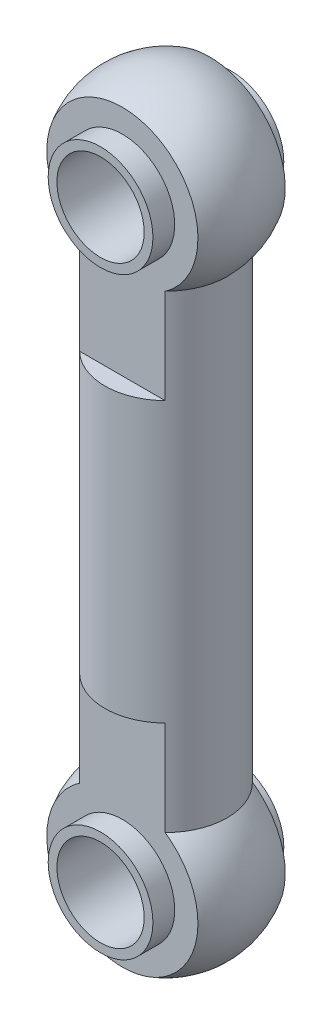
SolidWorks part; units mm, degrees
ref_plane "Front Plane" through (0, 0, 0) normal (0, 0, 1) x (1, 0, 0)
ref_plane "Top Plane" through (0, 0, 0) normal (0, 1, 0) x (1, 0, 0)
ref_plane "Right Plane" through (0, 0, 0) normal (1, 0, 0) x (0, 0, -1)
sketch "Sketch1" plane through (0, 0, 0) normal (0, 0, 1) x (1, 0, 0)
  line L0 (0, 0) -> (0, -7)
  line L1 (1.75, -17) -> (3.5, -17)
  line L2 (3.5, -17) -> (3.5, -3.5707)
  line L3 (0, 0) -> (0, 5)
  line L7 (0, -7) -> (1.75, -7)
  line L8 (1.75, -17) -> (1.75, -7)
  arc A0 (3.5, -3.5707) -> (0, 5) centre (0, 0) ccw
  dimension "D1" = 5
  dimension "D2" = 22
  dimension "D3" = 3.5
  dimension "D4" = 10
  dimension "D5" = 1.75
revolve "Revolve1" add sketch "Sketch1" angle 360 about L3
sketch "Sketch2" plane through (0, 0, 0) normal (0, 0, 1) x (1, 0, 0)
  circle A0 centre (0, 0) radius 2.5
  dimension "D1" = 5
extrude "Cut-Extrude1" cut sketch "Sketch2" against normal through all both and the other way through all
sketch "Sketch3" plane through (0, 0, 0) normal (0, 0, 1) x (1, 0, 0)
  circle A0 centre (0, 0) radius 2.5
ref_plane "Plane1" through (0, 0, 2.5) normal (0, 0, 1) x (1, 0, 0)
sketch "Sketch4" plane through (0, 0, 2.5) normal (0, 0, 1) x (1, 0, 0)
  line L1 (-6, -9) -> (6, -9)
  line L2 (-6, -9) -> (-6, 9)
  line L3 (-6, 9) -> (6, 9)
  line L4 (6, -9) -> (6, 9)
  line L5 (-6, -9) -> (6, 9) construction
  line L6 (-6, 9) -> (6, -9) construction
  point P0 (0, 0)
  dimension "D1" = 18
  dimension "D2" = 12
extrude "Cut-Extrude2" cut sketch "Sketch4" along normal up to next
mirror "Mirror1" about plane through (0, 0, 0) normal (0, 0, 1) of "Cut-Extrude2"
extrude "Extrude-Thin1" add sketch "Sketch3" along normal mid plane 7.5 thin
mirror "Mirror2" about plane through (1.75, -17, 0) normal (0, -1, 0) of bodies 105
